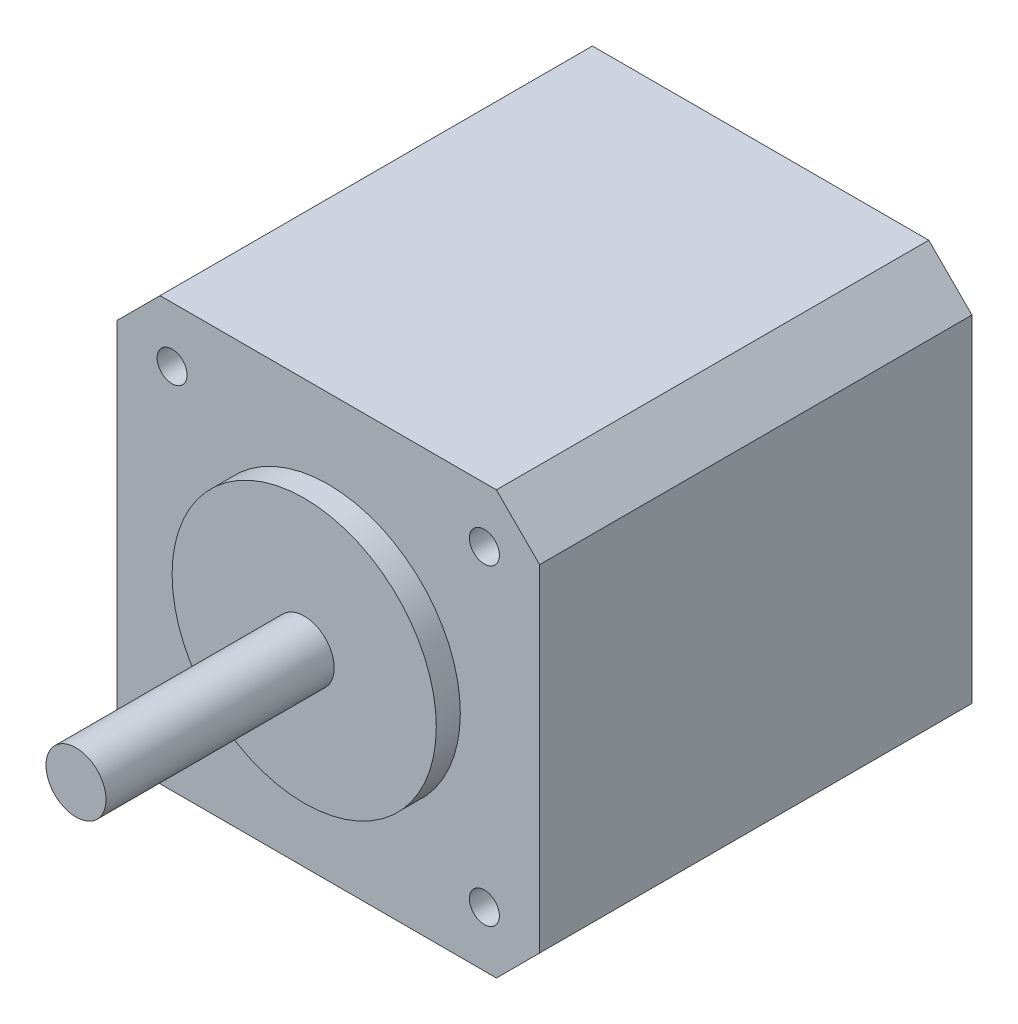
SolidWorks part; units mm, degrees
ref_plane "Front Plane" through (0, 0, 0) normal (0, 0, 1) x (1, 0, 0)
ref_plane "Top Plane" through (0, 0, 0) normal (0, 1, 0) x (1, 0, 0)
ref_plane "Right Plane" through (0, 0, 0) normal (1, 0, 0) x (0, 0, -1)
sketch "Sketch1" plane through (0, 0, 0) normal (0, 0, 1) x (1, 0, 0)
  line L0 (-17.6, 0) -> (17.6, 0) construction
  line L1 (0, 17.6) -> (0, -17.6) construction
  line L2 (-14.0038, -17.6) -> (14.0038, -17.6)
  line L3 (14.0038, -17.6) -> (17.6, -14.0038)
  line L4 (17.6, -14.0038) -> (17.6, 14.0038)
  line L5 (-17.6, -14.0038) -> (-17.6, 14.0038)
  line L6 (-14.0038, -17.6) -> (-17.6, -14.0038)
  line L7 (-14.0038, 17.6) -> (-17.6, 14.0038)
  line L8 (14.0038, 17.6) -> (17.6, 14.0038)
  line L9 (-14.0038, 17.6) -> (14.0038, 17.6)
  point P12 (0, -17.6)
  point P13 (-17.6, 0)
  point P15 (17.6, 0)
  dimension "D1" = 35.2
extrude "Boss-Extrude1" add sketch "Sketch1" against normal blind 36
sketch "Sketch2" plane through (0, 0, 0) normal (0, 0, 1) x (1, 0, 0)
  circle A0 centre (0, 0) radius 11
  dimension "D1" = 22
extrude "Boss-Extrude2" add sketch "Sketch2" along normal blind 2
sketch "Sketch3" plane through (0, 0, 0) normal (0, 0, 1) x (1, 0, 0)
  circle A0 centre (0, 0) radius 2.5
  dimension "D1" = 5
extrude "Boss-Extrude3" add sketch "Sketch3" along normal blind 21
hole_wizard "M3x0.5 Tapped Hole1" positions "Sketch5" profile "Sketch4" tap size "M3x0.5" standard "ANSI Metric"
sketch "Sketch5" plane through (0, 0, 0) normal (0, 0, 1) x (1, 0, 0)
  line L0 (13, -13) -> (-13, 13) construction
  line L2 (-13, -13) -> (13, 13) construction
  line L4 (-13, -13) -> (13, -13) construction
  line L5 (13, -13) -> (13, 13) construction
  point P0 (-13, -13)
  point P2 (13, -13)
  point P4 (13, 13)
  point P6 (-13, 13)
  dimension "D1" = 26
sketch "Sketch4" plane through (-13, -13, 0) normal (1, 0, 0) x (0, -1, 0)
  line L0 (0, 0) -> (0, 5.7511)
  line L1 (0, 5.7511) -> (1.25, 5)
  line L2 (1.25, 5) -> (1.25, 0)
  line L5 (1.25, 0) -> (0, 0)
  line L10 (0, 5.7511) -> (-1.25, 5) construction
  line L11 (0, -6.35) -> (0, 107.95) construction
  dimension "Tap Drill Dia." = 2.5
  dimension "Tap Drill Depth" = 5
  dimension "Drill Angle" = 118
cosmetic thread "Hole Thread1" parameters "D1"=3.5, "D2"=3
cosmetic thread "Hole Thread2" parameters "D1"=3.5, "D2"=3
cosmetic thread "Hole Thread3" parameters "D1"=3.5, "D2"=3
cosmetic thread "Hole Thread4" parameters "D1"=3.5, "D2"=3
